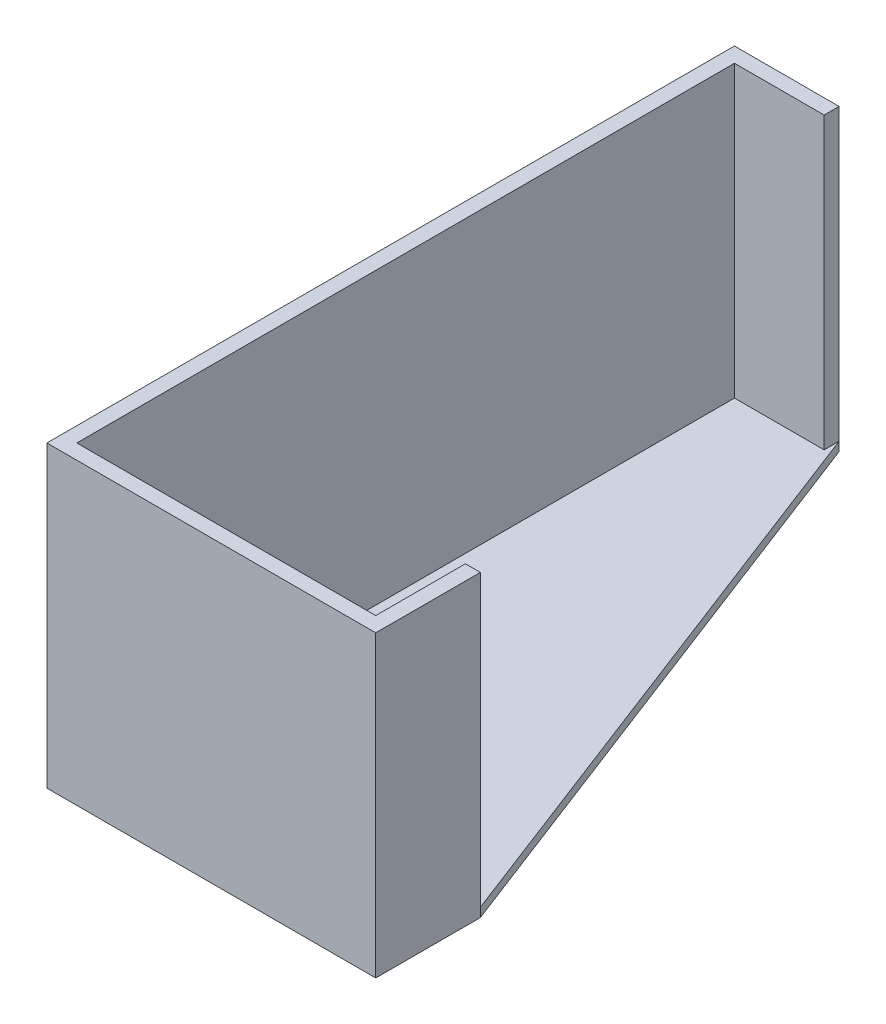
SolidWorks part; units mm, degrees
ref_plane "Piano frontale" through (0, 0, 0) normal (0, 0, 1) x (1, 0, 0)
ref_plane "Piano superiore" through (0, 0, 0) normal (0, 1, 0) x (1, 0, 0)
ref_plane "Piano destro" through (0, 0, 0) normal (1, 0, 0) x (0, 0, -1)
sketch "Schizzo1" plane through (0, 0, 0) normal (0, 1, 0) x (1, 0, 0)
  line L0 (100, 0) -> (0, 0)
  line L1 (0, 0) -> (0, 220)
  line L2 (100, 0) -> (100, 30)
  line L3 (0, 220) -> (30, 220)
  line L4 (105, -5) -> (105, 30)
  line L5 (105, -5) -> (-5, -5)
  line L6 (-5, -5) -> (-5, 225)
  line L7 (-5, 225) -> (30, 225)
  line L8 (30, 220) -> (30, 225)
  line L9 (100, 30) -> (105, 30)
  dimension "D1" = 220
  dimension "D2" = 100
  dimension "D3" = 30
  dimension "D4" = 30
  dimension "D5" = 5
extrude "Estrusione-Estrusione1" add sketch "Schizzo1" along normal blind 100
sketch "Schizzo2" plane through (0, 0, 0) normal (0, -1, 0) x (1, 0, 0)
  line L0 (30, -225) -> (-5, -225) construction
  line L1 (-5, -225) -> (-5, 5) construction
  line L2 (-5, 5) -> (105, 5) construction
  line L3 (105, 5) -> (105, -30) construction
  line L4 (30, -225) -> (-5, -225)
  line L5 (-5, -225) -> (-5, 5)
  line L6 (-5, 5) -> (105, 5)
  line L7 (105, 5) -> (105, -30)
  line L8 (105, -30) -> (30, -225)
extrude "Estrusione-Estrusione2" add sketch "Schizzo2" against normal blind 3
